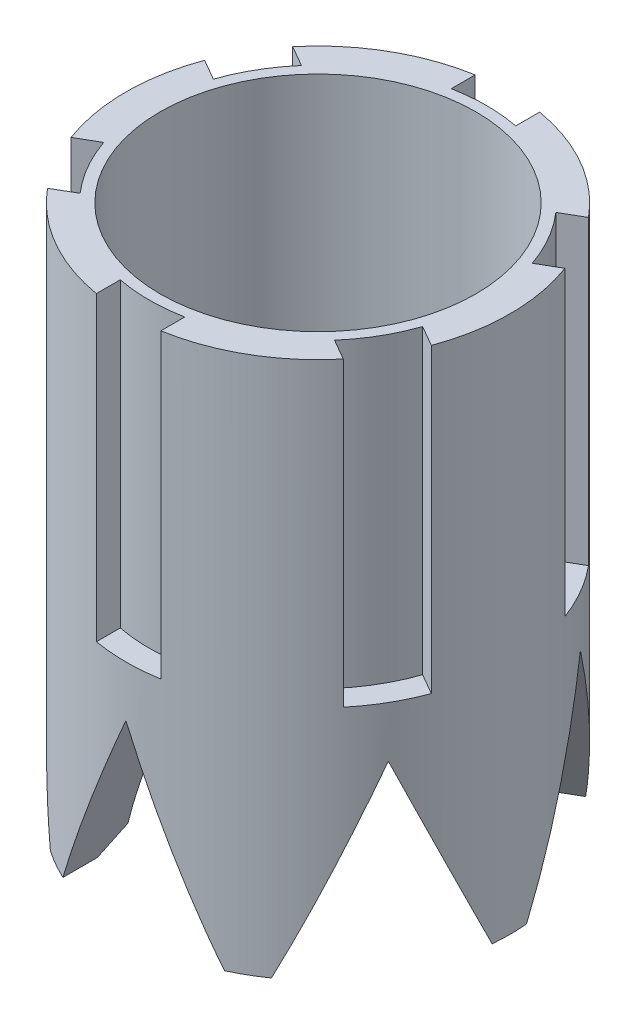
SolidWorks part; units mm, degrees
ref_plane "Front Plane" through (0, 0, 0) normal (0, 0, 1) x (1, 0, 0)
ref_plane "Top Plane" through (0, 0, 0) normal (0, 1, 0) x (1, 0, 0)
ref_plane "Right Plane" through (0, 0, 0) normal (1, 0, 0) x (0, 0, -1)
sketch "Sketch1" plane through (0, 0, 0) normal (0, 1, 0) x (1, 0, 0)
  circle A0 centre (0, 0) radius 3.67
  circle A1 centre (0, 0) radius 5.065
  dimension "D1" = 7.34
  dimension "D2" = 10.13
extrude "Boss-Extrude1" add sketch "Sketch1" along normal blind 14.17
sketch "Sketch2" plane through (0, 14.17, 0) normal (0, 1, 0) x (1, 0, 0)
  line L0 (0, 4.445) -> (5.8479, 4.445) construction
  line L1 (0, 5.065) -> (5.9071, 5.065) construction
  line L2 (0, -5.5715) -> (0, 5.5715) construction
  line L3 (-0.85, 4.363) -> (-0.85, 4.9932)
  line L4 (0.85, 4.363) -> (0.85, 4.9932)
  line L5 (3.3534, 2.9176) -> (3.8992, 3.2327)
  line L6 (4.2034, 1.4454) -> (4.7492, 1.7605)
  line L7 (4.2034, -1.4454) -> (4.7492, -1.7605)
  line L8 (3.3534, -2.9176) -> (3.8992, -3.2327)
  line L9 (0.85, -4.363) -> (0.85, -4.9932)
  line L10 (-0.85, -4.363) -> (-0.85, -4.9932)
  line L11 (-3.3534, -2.9176) -> (-3.8992, -3.2327)
  line L12 (-4.2034, -1.4454) -> (-4.7492, -1.7605)
  line L13 (-4.2034, 1.4454) -> (-4.7492, 1.7605)
  line L14 (-3.3534, 2.9176) -> (-3.8992, 3.2327)
  arc A0 (0.85, 4.363) -> (-0.85, 4.363) centre (0, 0) ccw
  circle A1 centre (0, 0) radius 5.065 construction
  arc A2 (-0.85, 4.9932) -> (0.85, 4.9932) centre (0, 0) cw
  arc A3 (4.2034, 1.4454) -> (3.3534, 2.9176) centre (0, 0) ccw
  arc A4 (3.8992, 3.2327) -> (4.7492, 1.7605) centre (0, 0) cw
  arc A5 (3.3534, -2.9176) -> (4.2034, -1.4454) centre (0, 0) ccw
  arc A6 (4.7492, -1.7605) -> (3.8992, -3.2327) centre (0, 0) cw
  arc A7 (-0.85, -4.363) -> (0.85, -4.363) centre (0, 0) ccw
  arc A8 (0.85, -4.9932) -> (-0.85, -4.9932) centre (0, 0) cw
  arc A9 (-4.2034, -1.4454) -> (-3.3534, -2.9176) centre (0, 0) ccw
  arc A10 (-3.8992, -3.2327) -> (-4.7492, -1.7605) centre (0, 0) cw
  arc A11 (-3.3534, 2.9176) -> (-4.2034, 1.4454) centre (0, 0) ccw
  arc A12 (-4.7492, 1.7605) -> (-3.8992, 3.2327) centre (0, 0) cw
  point P37 (0, 0)
  dimension "D1" = 0.62
  dimension "D2" = 0.85
  dimension "D3" = 0.85
  dimension "D4" = 6
extrude "Cut-Extrude1" cut sketch "Sketch2" against normal blind 7.95
sketch "Sketch3" plane through (0, 14.17, 0) normal (0, 1, 0) x (1, 0, 0)
  circle A0 centre (0, 0) radius 4.161
  dimension "D1" = 8.322
extrude "Cut-Extrude2" cut sketch "Sketch3" against normal blind 7.59
sketch "Sketch5" plane through (0, 0, 0) normal (0, 0, 1) x (1, 0, 0)
  line L0 (0, 4.88) -> (-2.13, 0)
  line L1 (0, -5.5715) -> (0, 5.5715) construction
  line L2 (5.5715, 0) -> (-5.5715, 0) construction
  line L3 (0, 4.88) -> (2.13, 0)
  line L4 (-2.13, 0) -> (2.13, 0)
  dimension "D1" = 2.13
  dimension "D2" = 2.13
  dimension "D3" = 4.88
extrude "Cut-Extrude4" cut sketch "Sketch5" against normal up to surface (5.065 mm away)
pattern_circular "CirPattern2" count 6 over 360 about axis through (0, 0, 0) along (0, 1, 0) of "Cut-Extrude4"
